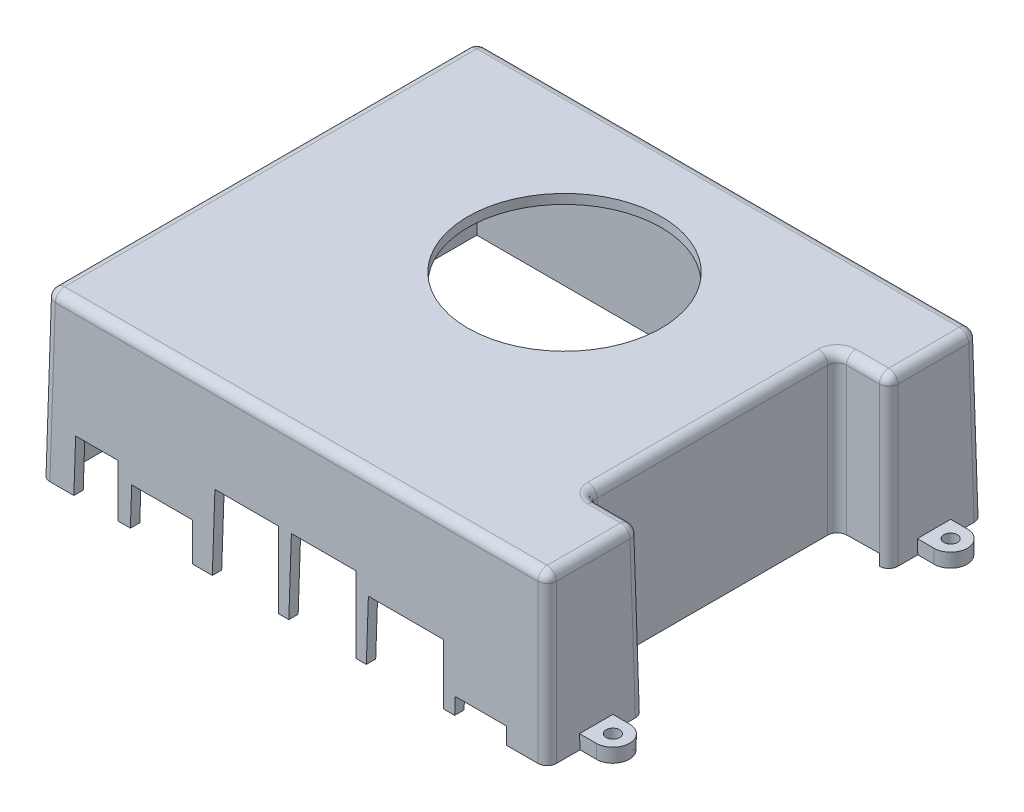
SolidWorks part; units mm, degrees
ref_plane "Front Plane" through (0, 0, 0) normal (0, 0, 1) x (1, 0, 0)
ref_plane "Top Plane" through (0, 0, 0) normal (0, 1, 0) x (1, 0, 0)
ref_plane "Right Plane" through (0, 0, 0) normal (1, 0, 0) x (0, 0, -1)
sketch "Sketch1" plane through (0, 0, 0) normal (0, 1, 0) x (1, 0, 0)
  line L0 (2.648, 0) -> (105.6416, 1.1453) construction
  line L1 (0, 0) -> (203, 0) construction
  line L2 (0, 0) -> (109, 0) construction
  line L3 (0, 0) -> (109, 0) construction
  line L16 (-7.0422, -20.1848) -> (101.9578, -20.1848) construction
  line L17 (-46.9758, 0) -> (1233.0242, 0) construction
  line L18 (5.0004, -4.0856) -> (114.0004, -4.0856) construction
  dimension "D1" = 109
  dimension "D2" = 109
  dimension "D3" = 109
sketch "Sketch2" plane through (0, 0, 0) normal (0, 1, 0) x (1, 0, 0)
  line L0 (108, -28.8752) -> (108, -49.6752)
  line L1 (0, 43.3248) -> (108, 43.3248)
  line L2 (0, 43.3248) -> (0, -49.6752)
  line L3 (0, -49.6752) -> (108, -49.6752)
  line L4 (108, 43.3248) -> (108, 23.1248)
  line L5 (97, 23.1248) -> (108, 23.1248)
  line L14 (97, 23.1248) -> (97, -28.8752)
  line L15 (97, -28.8752) -> (108, -28.8752)
  circle A0 centre (53.2, 8.8248) radius 20
  dimension "D5" = 40
  dimension "D1" = 93
  dimension "D2" = 108
  dimension "D3" = 34.5
  dimension "D4" = 53.2
  dimension "D6" = 20.8
  dimension "11" = 11
  dimension "52" = 52
extrude "Boss-Extrude1" add sketch "Sketch2" along normal blind 35 draft 1
shell "Shell2" thickness 2
sketch "Sketch3" plane through (0, 0, 0) normal (0, 0, 1) x (1, 0, 0)
  line L0 (-71.9332, 142.8467) -> (31.0668, 142.8467) construction
  line L1 (23.5647, -9.3009) -> (132.5647, -9.3009) construction
  line L2 (174.3333, 338) -> (871.6667, 338) construction
  line L3 (12.9834, 2.5116) -> (121.9834, 2.5116) construction
  dimension "D1" = 103
sketch "Sketch8" plane through (0, 0.8668, 49.6601) normal (0, 0.0175, 0.9998) x (1, 0, 0)
  line L0 (-4.1019, -0.867) -> (115.2168, -0.867) construction
  line L1 (0, -0.867) -> (109, -0.867)
  line L2 (0, -0.867) -> (0, 19.133)
  line L3 (0, 19.133) -> (109, 19.133)
  line L4 (109, -0.867) -> (109, 19.133)
  line L5 (7.3, -0.867) -> (16.3, -0.867)
  line L6 (7.3, -0.867) -> (7.3, 10.133)
  line L7 (7.3, 10.133) -> (16.3, 10.133)
  line L8 (16.3, -0.867) -> (16.3, 10.133)
  line L9 (19.3, -0.867) -> (32.3, -0.867)
  line L10 (19.3, -0.867) -> (19.3, 7.133)
  line L11 (19.3, 7.133) -> (32.3, 7.133)
  line L12 (32.3, -0.867) -> (32.3, 7.133)
  line L13 (36.9, -0.867) -> (50.4, -0.867)
  line L14 (36.9, -0.867) -> (36.9, 15.033)
  line L15 (36.9, 15.033) -> (50.4, 15.033)
  line L16 (50.4, -0.867) -> (50.4, 15.033)
  line L17 (53.2, -0.867) -> (66.95, -0.867)
  line L18 (53.2, -0.867) -> (53.2, 15.033)
  line L19 (53.2, 15.033) -> (66.95, 15.033)
  line L20 (66.95, -0.867) -> (66.95, 15.033)
  line L21 (69.6665, -0.867) -> (85.6665, -0.867)
  line L22 (69.6665, -0.867) -> (69.6665, 11.733)
  line L23 (69.6665, 11.733) -> (85.6665, 11.733)
  line L24 (85.6665, -0.867) -> (85.6665, 11.733)
  line L25 (88.3465, -0.867) -> (99.2465, -0.867)
  line L26 (88.3465, -0.867) -> (88.3465, 2.633)
  line L27 (88.3465, 2.633) -> (99.2465, 2.633)
  line L28 (99.2465, -0.867) -> (99.2465, 2.633)
  dimension "D1" = 20
  dimension "D2" = 109
  dimension "D3" = 0
  dimension "D4" = 11
  dimension "D5" = 9
  dimension "D6" = 7.3
  dimension "D7" = 3
  dimension "D8" = 13
  dimension "D9" = 8
  dimension "D10" = 4.6
  dimension "D11" = 13.5
  dimension "D12" = 15.9
  dimension "D13" = 13.75
  dimension "D14" = 15.9
  dimension "D15" = 2.8
  dimension "D16" = 16
  dimension "D17" = 12.6
  dimension "D18" = 2.7165
  dimension "D19" = 10.9
  dimension "D20" = 3.5
  dimension "D21" = 2.68
extrude "Cut-Extrude1" cut sketch "Sketch8" against normal up to vertex (2 mm away) contours L1 L8 L7 L6 | L1 L12 L11 L10 | L1 L16 L15 L14 | L1 L20 L19 L18 | L1 L24 L23 L22 | L1 L28 L27 L26 up to point (2.0003, 0, 47.6749)
sketch "Sketch10" plane through (0, 33, 0) normal (0, -1, 0) x (-1, 0, 0)
  circle A0 centre (-53.2, 8.8248) radius 23
  dimension "D1" = 46
extrude "Cut-Extrude2" cut sketch "Sketch10" along normal blind 35
sketch "Sketch12" plane through (96.9705, 1.6926, 0) normal (0.9998, 0.0175, 0) x (0, 0, -1)
  line L1 (-32.0752, -1.8929) -> (25.9248, -1.8929)
  line L2 (-32.0752, -1.8929) -> (-32.0752, 0.5071)
  line L3 (-32.0752, 0.5071) -> (25.9248, 0.5071)
  line L4 (25.9248, -1.8929) -> (25.9248, 0.5071)
  line L5 (-28.8752, -1.6929) -> (23.1248, -1.6929) construction
  dimension "D1" = 58
  dimension "D2" = 17.6
  dimension "D3" = 2.4
  dimension "0.2" = 0.2
extrude "Cut-Extrude5" cut sketch "Sketch12" along normal up to vertex (8.9983 mm away) and the other way up to vertex (2 mm away)
sketch "Sketch13" plane through (0, 0, 0) normal (0, -1, 0) x (-1, 0, 0)
  line L0 (-111.5, -42.6749) -> (-105.9997, -42.6749)
  line L1 (-111.4997, 29.3245) -> (-105.9997, 29.3245)
  line L2 (-111.5, -35.6749) -> (-105.9997, -35.6749)
  line L3 (-108, -49.6752) -> (-108, -28.8752) construction
  line L4 (-105.9997, -42.6749) -> (-105.9997, -35.6749)
  line L5 (-105.9997, -47.6749) -> (-105.9997, -28.8752) construction
  line L6 (-99.2465, -47.6749) -> (-105.9997, -47.6749) construction
  line L7 (-111.4997, 36.3245) -> (-105.9997, 36.3245)
  line L8 (-105.9997, 29.3245) -> (-105.9997, 36.3245)
  line L12 (-105.9997, 41.3245) -> (-2.0003, 41.3245) construction
  line L13 (-105.9997, 23.1248) -> (-105.9997, 41.3245) construction
  line L17 (3.5, 29.3245) -> (-2.0003, 29.3245)
  line L18 (3.5, 36.3245) -> (-2.0003, 36.3245)
  line L19 (-2.0003, 29.3245) -> (-2.0003, 36.3245)
  line L20 (-2.0003, 41.3245) -> (-2.0003, -47.6749) construction
  line L21 (0, 43.3248) -> (0, -49.6752) construction
  line L22 (3.5, -42.6749) -> (-2.0003, -42.6749)
  line L23 (3.5, -35.6749) -> (-2.0003, -35.6749)
  line L24 (-2.0003, -42.6749) -> (-2.0003, -35.6749)
  line L25 (-2.0003, -47.6749) -> (-7.3, -47.6749) construction
  arc A0 (-111.5, -35.6749) -> (-111.5, -42.6749) centre (-111.5, -39.1749) ccw
  circle A1 centre (-111.5, -39.1749) radius 1.5
  arc A2 (-111.4997, 36.3245) -> (-111.4997, 29.3245) centre (-111.4997, 32.8245) ccw
  circle A3 centre (-111.4997, 32.8245) radius 1.5
  arc A6 (3.5, 29.3245) -> (3.5, 36.3245) centre (3.5, 32.8245) ccw
  circle A7 centre (3.5, 32.8245) radius 1.5
  arc A8 (3.5, -42.6749) -> (3.5, -35.6749) centre (3.5, -39.1749) ccw
  circle A9 centre (3.5, -39.1749) radius 1.5
  dimension "D1" = 7
  dimension "D3" = 3
  dimension "D4" = 7
  dimension "D5" = 3
  dimension "D8" = 7
  dimension "D9" = 3
  dimension "D11" = 7
  dimension "D12" = 3
  dimension "D2" = 5
  dimension "D6" = 5
  dimension "D7" = 5.5
  dimension "D10" = 5
  dimension "D13" = 5
  dimension "D14" = 3.5
extrude "Boss-Extrude2" add sketch "Sketch13" against normal blind 3 draft 1 draft outward yes
fillet "Fillet1" radius 2 16 edges at (107.6945, 17.5, -23.4302) (96.6753, 18.5998, -23.4494) (96.6753, 18.5998, 29.1999) (107.6945, 17.5, 29.1807) (107.3891, 35, -33.2248) (107.6945, 17.5, 49.3698) (107.6945, 17.5, -43.0193) (0.3055, 17.5, -43.0193) (0.3055, 17.5, 49.3698) (101.8891, 35, -23.7357) (96.3891, 35, 2.8752) (101.8891, 35, 29.4862) (54, 35, -42.7138) (107.3891, 35, 39.2752) (54, 35, 49.0643) (0.6109, 35, 3.1752)
sketch "Sketch14" plane through (0, 0.8668, 49.6601) normal (0, 0.0175, 0.9998) x (1, 0, 0)
  line L0 (7.3, 10.133) -> (7.108, -0.867)
  line L1 (1.9997, -0.867) -> (7.3, -0.867) construction
  line L2 (7.3, 10.133) -> (16.3, 10.133)
  line L3 (16.3, 10.133) -> (16.492, -0.867)
  line L4 (16.3, -0.867) -> (19.3, -0.867) construction
  line L5 (16.492, -0.867) -> (7.108, -0.867)
  line L6 (19.3, 7.133) -> (32.3, 7.133)
  line L7 (19.3, 7.133) -> (32.3, 7.133) construction
  line L8 (32.3, -0.867) -> (32.3, 7.133) construction
  line L9 (32.3, 7.133) -> (32.4396, -0.867)
  line L10 (32.3, -0.867) -> (36.9, -0.867) construction
  line L11 (19.1604, -0.867) -> (19.3, 7.133)
  line L12 (19.1604, -0.867) -> (32.4396, -0.867)
  line L13 (36.6225, -0.867) -> (36.9, 15.033)
  line L14 (36.9, 15.033) -> (50.4, 15.033)
  line L15 (50.4, 15.033) -> (50.6775, -0.867)
  line L16 (50.4, -0.867) -> (53.2, -0.867) construction
  line L17 (50.6775, -0.867) -> (36.6225, -0.867)
  line L18 (66.95, 15.033) -> (67.2275, -0.867)
  line L19 (66.95, -0.867) -> (69.6665, -0.867) construction
  line L20 (67.2275, -0.867) -> (52.9225, -0.867)
  line L21 (52.9225, -0.867) -> (53.2, 15.033)
  line L22 (53.2, 15.033) -> (66.95, 15.033)
  line L23 (69.6665, 11.733) -> (69.4489, -0.867)
  line L24 (69.6665, -0.867) -> (69.6665, 11.733) construction
  line L25 (69.4489, -0.867) -> (85.8864, -0.867)
  line L26 (85.6665, -0.867) -> (88.3465, -0.867) construction
  line L27 (85.8864, -0.867) -> (85.6665, 11.733)
  line L28 (85.6665, 11.733) -> (69.6665, 11.733)
  line L29 (88.2854, -0.867) -> (88.3465, 2.633)
  line L30 (88.3465, 2.633) -> (99.2465, 2.633)
  line L31 (99.2465, 2.633) -> (99.3076, -0.867)
  line L32 (99.2465, -0.867) -> (106.0003, -0.867) construction
  line L33 (99.3076, -0.867) -> (88.2854, -0.867)
  dimension "D1" = 9.384
  dimension "D2" = 13.2793
  dimension "D3" = 14.0551
extrude "Cut-Extrude6" cut sketch "Sketch14" against normal blind 3
